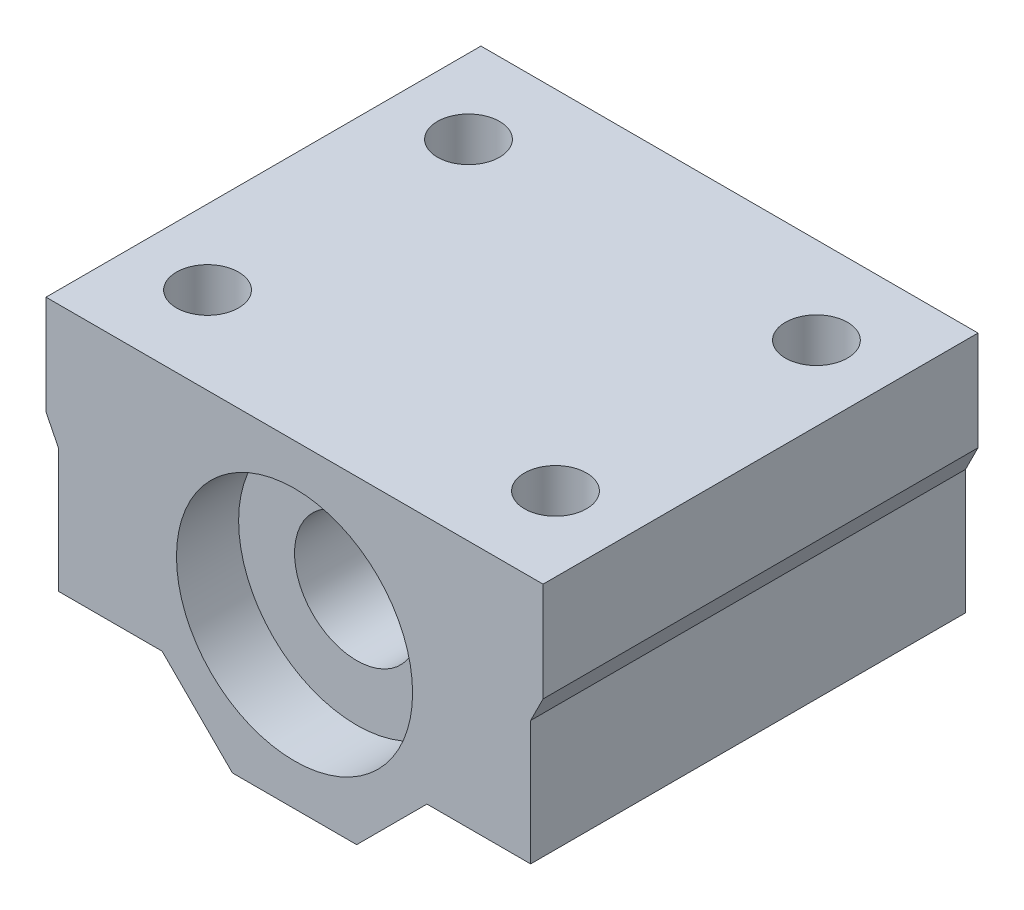
SolidWorks part; units mm, degrees
ref_plane "Plan de face" through (0, 0, 0) normal (0, 0, 1) x (1, 0, 0)
ref_plane "Plan de dessus" through (0, 0, 0) normal (0, 1, 0) x (1, 0, 0)
ref_plane "Plan de droite" through (0, 0, 0) normal (1, 0, 0) x (0, 0, -1)
sketch "Sketch2" plane through (0, 0, 0) normal (0, 0, 1) x (1, 0, 0)
  line L0 (-5, 0) -> (5, 0)
  line L1 (5, 0) -> (10.6569, 5.6569)
  line L2 (10.6569, 5.6569) -> (19, 5.6569)
  line L3 (19, 5.6569) -> (19, 15.6569)
  line L4 (19, 15.6569) -> (20, 17.6569)
  line L5 (20, 17.6569) -> (20, 25.6569)
  line L6 (20, 25.6569) -> (-20, 25.6569)
  line L7 (0, 25.6569) -> (0, 0) construction
  line L8 (-20, 17.6569) -> (-20, 25.6569)
  line L9 (-19, 15.6569) -> (-20, 17.6569)
  line L10 (-19, 5.6569) -> (-19, 15.6569)
  line L11 (-10.6569, 5.6569) -> (-19, 5.6569)
  line L12 (-5, 0) -> (-10.6569, 5.6569)
  line L13 (0, 0) -> (52.2633, 0) construction
  dimension "D1" = 10
  dimension "D2" = 8
  dimension "D3" = 45
  dimension "D4" = 20
  dimension "D5" = 10
  dimension "D6" = 8
  dimension "D7" = 1
  dimension "D8" = 40
extrude "Boss-Extrude1" add sketch "Sketch2" along normal blind 35
sketch "Sketch3" plane through (0, 0, 35) normal (0, 0, 1) x (1, 0, 0)
  line L0 (20, 25.6569) -> (-20, 25.6569) construction
  line L1 (-5, 0) -> (5, 0) construction
  line L2 (-5, 0) -> (-5, 25.6569) construction
  line L3 (-5, 25.6569) -> (5, 25.6569) construction
  line L4 (5, 0) -> (5, 25.6569) construction
  line L5 (-5, 25.6569) -> (5, 0) construction
  line L6 (5, 25.6569) -> (-5, 0) construction
  circle A0 centre (0, 12.8284) radius 9.5
  point P9 (0, 12.8284)
  dimension "D1" = 19
extrude "Cut-Extrude1" cut sketch "Sketch3" against normal blind 5 contours A0
sketch "Sketch4" plane through (0, 0, 30) normal (0, 0, 1) x (1, 0, 0)
  circle A0 centre (0, 12.8284) radius 5
  dimension "D1" = 10
extrude "Cut-Extrude2" cut sketch "Sketch4" against normal through all contours A0
ref_plane "Plane1" through (0, 0, 17.5) normal (0, 0, 1) x (1, 0, 0)
mirror "Mirror1" about plane through (0, 0, 17.5) normal (0, 0, 1) of "Cut-Extrude1"
sketch "Sketch5" plane through (0, 25.6569, 0) normal (0, 1, 0) x (1, 0, 0)
  line L0 (-20, -17.5) -> (20, -17.5) construction
  line L1 (-20, -35) -> (-20, 0) construction
  line L2 (20, -35) -> (20, 0) construction
  line L3 (-14, -7) -> (14, -7) construction
  line L5 (0, 0) -> (0, -35) construction
  line L6 (20, -35) -> (-20, -35) construction
  circle A0 centre (-14, -7) radius 2.5
  circle A1 centre (14, -7) radius 2.5
  circle A2 centre (14, -28) radius 2.5
  circle A3 centre (-14, -28) radius 2.5
  point P10 (0, -7)
  dimension "D1" = 5
  dimension "D3" = 5
  dimension "D2" = 28
  dimension "D4" = 21
extrude "Cut-Extrude3" cut sketch "Sketch5" against normal through all
